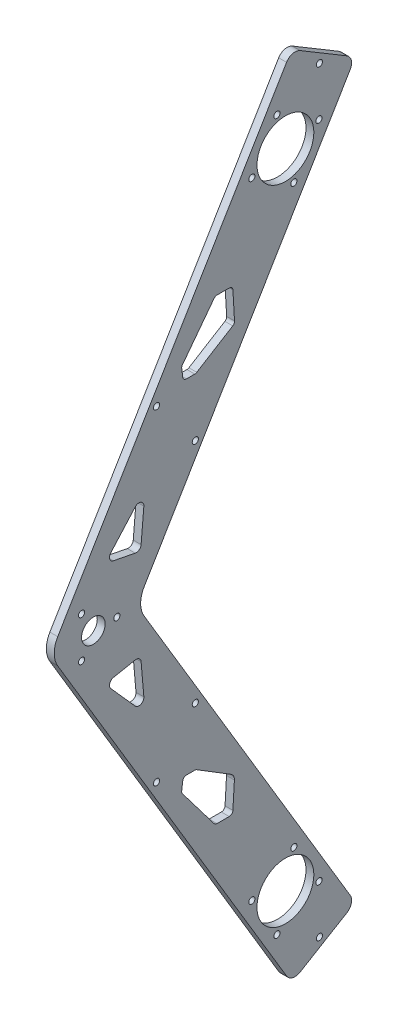
SolidWorks part; units mm, degrees
ref_plane "Front Plane" through (0, 0, 0) normal (1, 0, 0) x (0, 1, 0)
ref_plane "Top Plane" through (0, 0, 0) normal (0, 0, 1) x (0, 1, 0)
ref_plane "Right Plane" through (0, 0, 0) normal (0, 1, 0) x (-1, 0, 0)
sketch "sketch" plane through (0, 0, 0) normal (1, 0, 0) x (0, 1, 0)
  line L0 (260, 0) -> (-260, 0) construction
  line L1 (0, 0) -> (0, 280) construction
  line L2 (0, 280) -> (0, 197.29) construction
  line L3 (0, 197.29) -> (260, 0) construction
  line L4 (0, 197.29) -> (-260, 0) construction
  line L5 (0, 0) -> (130, 98.645) construction
  line L6 (130, 98.645) -> (130, 119.61) construction
  line L7 (130, 98.645) -> (130, 77.68) construction
  line L8 (130, 77.68) -> (0, 0) construction
  line L9 (130, 77.68) -> (260, 0) construction
  circle A0 centre (0, 0) radius 65 construction
  circle A1 centre (260, 0) radius 65 construction
  circle A2 centre (-260, 0) radius 65 construction
  point P4 (0, 0)
  dimension "D1" = 130
  dimension "D2" = 130
  dimension "D4" = 130
  dimension "D5" = 280
  dimension "D3" = 260
  dimension "D6" = 82.71
  dimension "D7" = 20.965
  dimension "D8" = 20.965
sketch "bogie base" plane through (0, 0, 0) normal (1, 0, 0) x (0, 1, 0)
  line L1 (260, 0) -> (-260, 0) construction
  line L3 (-25.7527, -15.3882) -> (9.8719, 5.8988) construction
  line L9 (-31.3951, -5.9456) -> (-20.1104, -24.8309)
  line L15 (285.7527, -15.3882) -> (234.2473, 15.3882) construction
  line L16 (130, 77.68) -> (260, 0) construction
  line L17 (291.3951, -5.9456) -> (280.1104, -24.8309)
  line L25 (124.8706, 92.0889) -> (-30.0131, -0.4601)
  line L26 (124.8706, 57.1411) -> (-14.6249, -26.2128)
  line L27 (135.1294, 57.1411) -> (274.6249, -26.2128)
  line L28 (135.1294, 92.0889) -> (290.0131, -0.4601)
  circle A0 centre (260, 0) radius 11.5 construction
  circle A1 centre (0, 0) radius 11.5 construction
  arc A2 (124.8706, 57.1411) -> (135.1294, 57.1411) centre (130, 48.5569) cw
  arc A3 (124.8706, 92.0889) -> (135.1294, 92.0889) centre (130, 83.5046) cw
  arc A4 (291.3951, -5.9456) -> (290.0131, -0.4601) centre (287.9614, -3.8938) ccw
  arc A5 (280.1104, -24.8309) -> (274.6249, -26.2128) centre (276.6767, -22.7791) cw
  arc A6 (-14.6249, -26.2128) -> (-20.1104, -24.8309) centre (-16.6767, -22.7791) cw
  arc A7 (-31.3951, -5.9456) -> (-30.0131, -0.4601) centre (-27.9614, -3.8938) cw
  point P4 (130, 98.645)
  point P12 (0, 0)
  point P14 (-25.7527, -15.3882)
  point P18 (260, 0)
  point P19 (0, 0)
  point P24 (130, 98.645)
  point P26 (260, 0)
  point P29 (285.7527, -15.3882)
  point P33 (130, 60.2061)
  point P35 (130, 77.68)
  point P37 (130, 95.1539)
  point P38 (130, 77.68)
  point P41 (130, 98.645)
  point P43 (293.4468, -2.5119)
  point P46 (278.0586, -28.2646)
  point P49 (-18.0586, -28.2646)
  point P52 (-33.4468, -2.5119)
  dimension "D11" = 23
  dimension "D12" = 118.28
  dimension "D2" = 23
  dimension "D14" = 10
  dimension "D15" = 10
  dimension "D16" = 4
  dimension "D3" = 90
  dimension "D4" = 30
  dimension "D5" = 30
  dimension "D6" = 90
  dimension "D7" = 30
  dimension "D8" = 30
  dimension "D9" = 190.4034
  dimension "D10" = 34.9478
  dimension "D13" = 241.72
extrude "extrude-base" add sketch "bogie base" along normal blind 3.18
sketch "Sketch4" plane through (0, 0, 0) normal (1, 0, 0) x (0, 1, 0)
  circle A0 centre (260, 0) radius 11.5
  circle A1 centre (0, 0) radius 11.5
  dimension "D1" = 23
  dimension "D2" = 23
extrude "Cut-motor holes\\" cut sketch "Sketch4" along normal blind 3.18
sketch "Sketch5" plane through (0, 0, 0) normal (1, 0, 0) x (0, 1, 0)
  line L0 (-14.6249, -26.2128) -> (124.8706, 57.1411) construction
  line L2 (130, 93.5046) -> (130, 58.5569) construction
  circle A1 centre (3.4194, 13.576) radius 1.25
  circle A2 centre (-3.4194, -13.576) radius 1.25
  circle A3 centre (13.5774, -3.4198) radius 1.25
  circle A4 centre (-13.5774, 3.4198) radius 1.25
  circle A11 centre (0, 0) radius 11.5 construction
  arc A12 (135.1294, 92.0889) -> (124.8706, 92.0889) centre (130, 83.5046) ccw construction
  arc A13 (135.1294, 57.1411) -> (124.8706, 57.1411) centre (130, 48.5569) ccw construction
  circle A14 centre (260, 0) radius 11.5 construction
  circle A15 centre (273.5774, 3.4198) radius 1.25
  circle A16 centre (246.4226, -3.4198) radius 1.25
  circle A17 centre (263.4194, -13.576) radius 1.25
  circle A18 centre (256.5806, 13.576) radius 1.25
  point P13 (0, 0)
  point P22 (0, 0)
  point P33 (260, 0)
  point P34 (260, 0)
  dimension "D1" = 2.5
  dimension "D2" = 2.5
  dimension "D3" = 2.5
  dimension "D4" = 2.5
  dimension "D13" = 5.1
  dimension "D5" = 23
  dimension "D6" = 28
  dimension "D7" = 14
  dimension "D8" = 19.8
  dimension "D9" = 19.8
  dimension "D10" = 19.8
  dimension "D11" = 19.8
  dimension "D12" = 5.1
extrude "motor support holes" cut sketch "Sketch5" along normal blind 3.18
sketch "Sketch6" plane through (0, 0, 0) normal (1, 0, 0) x (0, 1, 0)
  line L0 (130, 82.445) -> (130, 66.92) construction
  line L2 (-25.7527, -15.3882) -> (-23.0229, -13.7571) construction
  line L3 (-25.7527, -15.3882) -> (9.8719, 5.8988) construction
  line L5 (-30.717, -0.8807) -> (-15.3288, -26.6334) construction
  line L6 (124.8706, 57.1411) -> (-14.6249, -26.2128) construction
  line L7 (-25.3312, -9.8942) -> (-20.7147, -17.62) construction
  line L9 (-31.3951, -5.9456) -> (-20.1104, -24.8309) construction
  line L10 (106.8543, 81.3234) -> (122.2425, 55.5707) construction
  line L12 (-23.0229, -13.7571) -> (18.1814, 10.8641) construction
  line L13 (130, 77.68) -> (0, 0) construction
  line L14 (130, 77.68) -> (18.1814, 10.8641) construction
  line L15 (66.3966, 57.1484) -> (81.7848, 31.3957) construction
  line L16 (10.4873, 23.7405) -> (25.8755, -2.0123) construction
  line L17 (77.9536, 46.5803) -> (70.2278, 41.9638) construction
  line L18 (62.5337, 54.8402) -> (77.9219, 29.0875) construction
  line L19 (70.2595, 59.4566) -> (85.6477, 33.7039) construction
  line L20 (62.5337, 54.8402) -> (64.1648, 52.1104) construction
  line L21 (130, 77.68) -> (130, 68.17) construction
  line L22 (130, 68.17) -> (121.7723, 82.4492) construction
  line L23 (121.7723, 82.4492) -> (138.2488, 82.437) construction
  line L24 (138.2488, 82.437) -> (130, 68.17) construction
  line L25 (130, 77.68) -> (121.7723, 82.4492) construction
  circle A19 centre (64.1648, 52.1104) radius 1.25
  circle A22 centre (84.0166, 36.4337) radius 1.25
  circle A23 centre (130, 77.68) radius 4.765
  circle A24 centre (130, 68.17) radius 1.25
  circle A25 centre (121.7723, 82.4492) radius 1.25
  circle A26 centre (138.2488, 82.437) radius 1.25
  circle A27 centre (175.9834, 36.4337) radius 1.25
  circle A29 centre (195.8352, 52.1104) radius 1.25
  circle A33 centre (-23.0229, -13.7571) radius 1.25
  circle A34 centre (283.0229, -13.7571) radius 1.25
  point P12 (-23.0229, -13.7571)
  point P15 (-23.0229, -13.7571)
  point P25 (114.5484, 68.4471)
  point P32 (74.0907, 44.272)
  point P35 (18.1814, 10.8641)
  point P38 (74.0907, 44.272)
  point P41 (70.2278, 41.9638)
  point P44 (77.9536, 46.5803)
  dimension "D5" = 18
  dimension "D8" = 48
  dimension "D9" = 30
  dimension "D10" = 4.5
  dimension "D1" = 3.18
  dimension "D3" = 9
  dimension "D11" = 2.5
  dimension "D13" = 9.53
  dimension "D14" = 2.5
  dimension "D20" = 2.5
  dimension "D21" = 2.5
  dimension "D22" = 19.6131
  dimension "D23" = 2.5
  dimension "D24" = 2.7298
  dimension "D25" = 25.2952
  dimension "D26" = 2.5
  dimension "D6" = 30
  dimension "D7" = 30.86
  dimension "D12" = 3.18
  dimension "D15" = 9.51
  dimension "D16" = 16.48
  dimension "D17" = 16.4764
  dimension "D18" = 16.48
  dimension "D19" = 9.51
extrude "support holes" cut sketch "Sketch6" along normal blind 3.18
sketch "Sketch7" plane through (0, 0, 0) normal (1, 0, 0) x (0, 1, 0)
  line L8 (130, 77.68) -> (0, 0) construction
  line L10 (54.884, 41.6464) -> (38.0344, 28.8608)
  line L11 (0, 0) -> (130, 98.645) construction
  line L12 (37.4411, 27.6659) -> (37.4411, 22.7346)
  line L13 (38.8533, 21.2372) -> (49.1659, 20.6321)
  line L14 (51.8962, 22.054) -> (60.3984, 35.8618)
  line L15 (60.6211, 36.6482) -> (60.6211, 40.0362)
  line L16 (59.3068, 41.5246) -> (55.9763, 41.9399)
  line L23 (130, 93.5046) -> (130, 58.5569) construction
  line L30 (200.6932, 41.5246) -> (204.0237, 41.9399)
  line L31 (199.3789, 36.6482) -> (199.3789, 40.0362)
  line L32 (208.5739, 21.2905) -> (199.6016, 35.8618)
  line L33 (221.1467, 21.2372) -> (209.939, 20.5796)
  line L34 (222.5589, 27.6659) -> (222.5589, 22.7346)
  line L35 (205.116, 41.6464) -> (221.9656, 28.8608)
  line L45 (106.2616, 70.6588) -> (95.1131, 60.7377)
  line L46 (96.6148, 57.251) -> (109.5021, 58.3648)
  line L47 (111.292, 60.7448) -> (109.5533, 69.5521)
  line L48 (148.708, 60.7448) -> (150.4467, 69.5521)
  line L49 (163.3852, 57.251) -> (150.4979, 58.3648)
  line L50 (153.7384, 70.6588) -> (164.8869, 60.7377)
  arc A9 (37.4411, 22.7346) -> (38.8533, 21.2372) centre (38.9411, 22.7346) ccw
  arc A10 (38.0344, 28.8608) -> (37.4411, 27.6659) centre (38.9411, 27.6659) ccw
  arc A12 (60.3984, 35.8618) -> (60.6211, 36.6482) centre (59.1211, 36.6482) ccw
  arc A13 (60.6211, 40.0362) -> (59.3068, 41.5246) centre (59.1211, 40.0362) ccw
  arc A14 (55.9763, 41.9399) -> (54.884, 41.6464) centre (55.7907, 40.4515) ccw
  arc A21 (135.1294, 92.0889) -> (124.8706, 92.0889) centre (130, 83.5046) ccw construction
  arc A22 (135.1294, 57.1411) -> (124.8706, 57.1411) centre (130, 48.5569) ccw construction
  arc A29 (204.0237, 41.9399) -> (205.116, 41.6464) centre (204.2093, 40.4515) cw
  arc A30 (199.3789, 40.0362) -> (200.6932, 41.5246) centre (200.8789, 40.0362) cw
  arc A31 (199.6016, 35.8618) -> (199.3789, 36.6482) centre (200.8789, 36.6482) cw
  arc A32 (209.939, 20.5796) -> (208.5739, 21.2905) centre (209.8512, 22.077) cw
  arc A33 (221.9656, 28.8608) -> (222.5589, 27.6659) centre (221.0589, 27.6659) cw
  arc A34 (222.5589, 22.7346) -> (221.1467, 21.2372) centre (221.0589, 22.7346) cw
  arc A44 (51.8962, 22.054) -> (49.1659, 20.6321) centre (49.3417, 23.6269) cw
  arc A45 (106.2616, 70.6588) -> (109.5533, 69.5521) centre (107.5912, 69.1648) cw
  arc A46 (109.5021, 58.3648) -> (111.292, 60.7448) centre (109.3299, 60.3574) ccw
  arc A47 (95.1131, 60.7377) -> (96.6148, 57.251) centre (96.4426, 59.2436) ccw
  arc A48 (164.8869, 60.7377) -> (163.3852, 57.251) centre (163.5574, 59.2436) cw
  arc A49 (150.4979, 58.3648) -> (148.708, 60.7448) centre (150.6701, 60.3574) cw
  arc A50 (153.7384, 70.6588) -> (150.4467, 69.5521) centre (152.4088, 69.1648) ccw
  point P48 (37.4411, 28.4106)
  point P53 (60.6211, 36.2235)
  point P58 (55.3704, 42.0155)
  point P144 (204.6296, 42.0155)
  point P145 (199.3789, 36.2235)
  point P146 (222.5589, 28.4106)
  dimension "D1" = 2
  dimension "D2" = 14.9238
  dimension "D3" = 1.5
  dimension "D4" = 12.8873
  dimension "D5" = 3
  dimension "D6" = 8.9774
extrude "Cut-lightening holes" cut sketch "Sketch7" along normal blind 3.18
